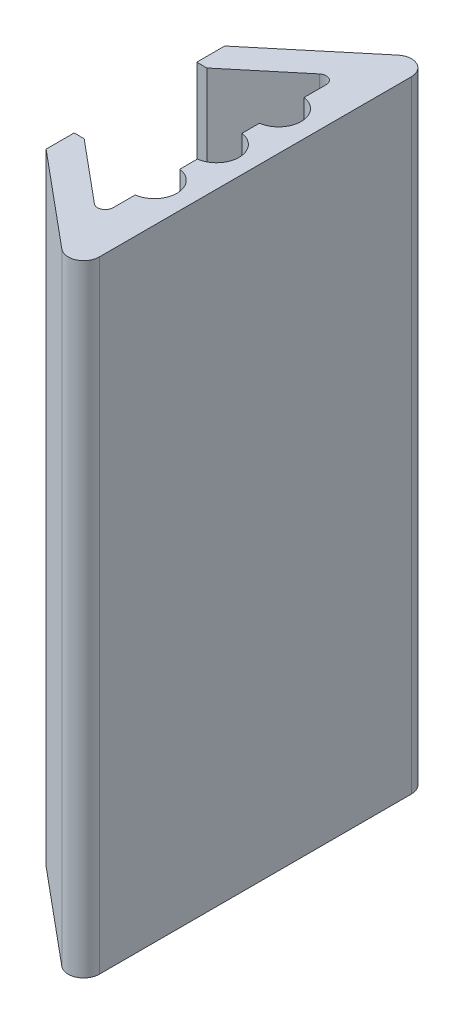
SolidWorks part; units mm, degrees
ref_plane "Front Plane" through (0, 0, 0) normal (0, 0, 1) x (1, 0, 0)
ref_plane "Top Plane" through (0, 0, 0) normal (0, 1, 0) x (1, 0, 0)
ref_plane "Right Plane" through (0, 0, 0) normal (1, 0, 0) x (0, 0, -1)
sketch "Sketch1" plane through (0, 0, 0) normal (0, 1, 0) x (1, 0, 0)
  line L0 (18.5518, 11.5) -> (18.5518, 7.9)
  line L1 (19.8458, -7.8922) -> (18.5518, -7.8922)
  line L2 (18.5518, -7.8922) -> (18.5518, -11.5)
  line L10 (18.5518, 11.5) -> (30.7196, 21.6399)
  line L11 (34, 20.1034) -> (34, -20.1034)
  line L12 (30.7196, -21.6399) -> (18.5518, -11.5)
  line L14 (29.4, -13.719) -> (29.4, -10.8723)
  line L15 (29.4, -5.1277) -> (29.4, -2.8723)
  line L16 (29.4, 2.8723) -> (29.4, 5.1277)
  line L17 (29.4, 10.8723) -> (29.4, 13.719)
  line L19 (29.4, 15) -> (29, 15)
  line L20 (27.7598, 14.4872) -> (19.8552, 7.9)
  line L21 (19.8552, 7.9) -> (18.5518, 7.9)
  line L23 (19.8458, -7.8922) -> (27.7598, -14.4872)
  arc A3 (29.4, -10.8723) -> (29.4, -5.1277) centre (29, -8) ccw
  arc A4 (29.4, -2.8723) -> (29.4, 2.8723) centre (29, 0) ccw
  arc A5 (29.4, 5.1277) -> (29.4, 10.8723) centre (29, 8) ccw
  arc A6 (34, -20.1034) -> (30.7196, -21.6399) centre (32, -20.1034) cw
  arc A7 (34, 20.1034) -> (30.7196, 21.6399) centre (32, 20.1034) ccw
  arc A8 (29.4, 13.719) -> (27.7598, 14.4872) centre (28.4, 13.719) ccw
  arc A9 (29.4, -13.719) -> (27.7598, -14.4872) centre (28.4, -13.719) cw
  point P0 (29.4, 12.2956)
  dimension "D5" = 4.6
  dimension "D6" = 2.9
  dimension "D7" = 2.9
  dimension "D18" = 2
  dimension "D21" = 1
  dimension "D22" = 1
  dimension "D8" = 2.9
  dimension "D4" = 3.6
  dimension "D9" = 3.6
  dimension "D12" = 15
extrude "Boss-Extrude1" add sketch "Sketch1" along normal blind 80
